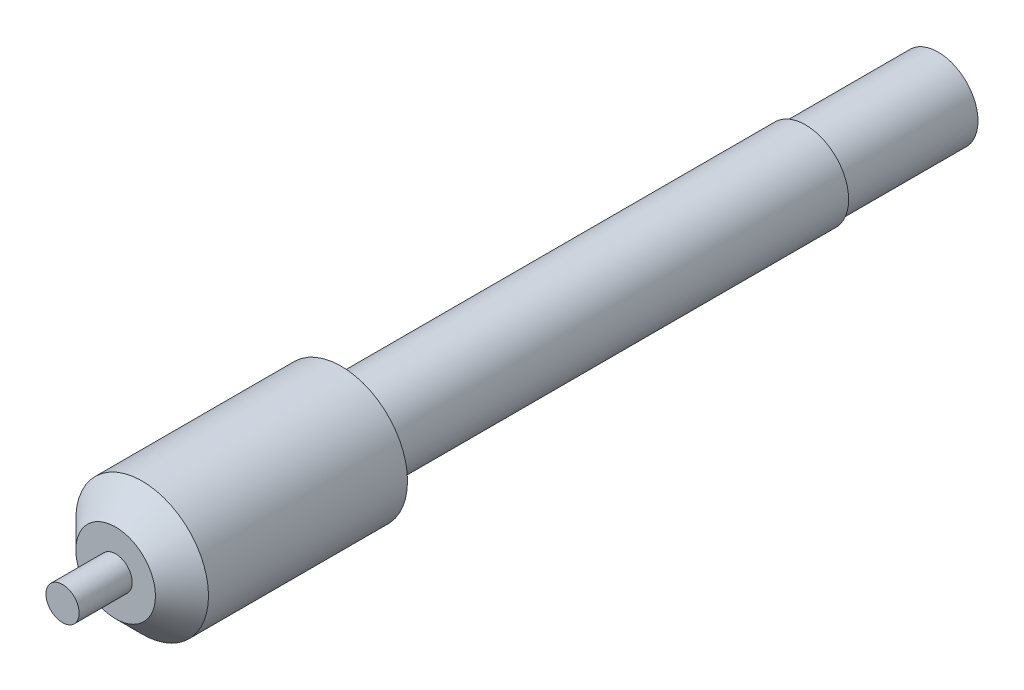
SolidWorks part; units mm, degrees
ref_plane "Alzado" through (0, 0, 0) normal (0, 0, 1) x (1, 0, 0)
ref_plane "Planta" through (0, 0, 0) normal (0, 1, 0) x (1, 0, 0)
ref_plane "Vista lateral" through (0, 0, 0) normal (1, 0, 0) x (0, 0, -1)
sketch "Croquis1" plane through (0, 0, 0) normal (0, 0, 1) x (1, 0, 0)
  circle A0 centre (0, 0) radius 3
  dimension "D1" = 6
extrude "Saliente-Extruir1" add sketch "Croquis1" along normal blind 10
sketch "Croquis2" plane through (0, 0, 10) normal (0, 0, 1) x (1, 0, 0)
  circle A0 centre (0, 0) radius 3.25
  dimension "D1" = 6.5
extrude "Saliente-Extruir2" add sketch "Croquis2" along normal blind 35
sketch "Croquis3" plane through (0, 0, 45) normal (0, 0, 1) x (1, 0, 0)
  circle A0 centre (0, 0) radius 5
  dimension "D1" = 10
extrude "Saliente-Extruir3" add sketch "Croquis3" along normal blind 17
chamfer "Chaflán1" distance 2 angle 45 1 edges at (5, 0, 62)
sketch "Croquis4" plane through (0, 0, 62) normal (0, 0, 1) x (1, 0, 0)
  circle A0 centre (0, 0) radius 1.25
  dimension "D1" = 2.5
extrude "Saliente-Extruir4" add sketch "Croquis4" along normal blind 4
